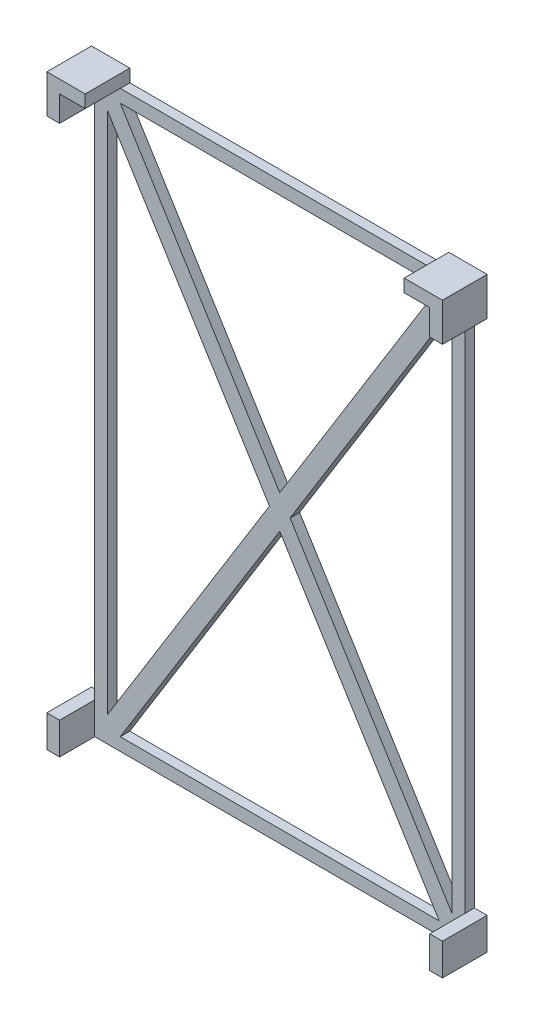
SolidWorks part; units mm, degrees
ref_plane "Alzado" through (0, 0, 0) normal (0, 0, 1) x (1, 0, 0)
ref_plane "Planta" through (0, 0, 0) normal (0, 1, 0) x (1, 0, 0)
ref_plane "Vista lateral" through (0, 0, 0) normal (1, 0, 0) x (0, 0, -1)
sketch "Croquis1" plane through (0, 0, 0) normal (0, 0, 1) x (1, 0, 0)
  line L1 (-96.0018, 29.9441) -> (-38.0018, 29.9441)
  line L2 (-96.0018, 29.9441) -> (-96.0018, -60.0559)
  line L3 (-96.0018, -60.0559) -> (-38.0018, -60.0559)
  line L4 (-38.0018, 29.9441) -> (-38.0018, -60.0559)
  line L5 (-94.0018, 27.9441) -> (-40.0018, 27.9441)
  line L6 (-94.0018, 27.9441) -> (-94.0018, -58.0559)
  line L7 (-94.0018, -58.0559) -> (-40.0018, -58.0559)
  line L8 (-40.0018, 27.9441) -> (-40.0018, -58.0559)
  dimension "D1" = 90
  dimension "D2" = 58
  dimension "D3" = 2
  dimension "D4" = 2
  dimension "D5" = 2
  dimension "D6" = 2
extrude "Saliente-Extruir1" add sketch "Croquis1" along normal blind 1.5
sketch "Croquis2" plane through (0, 0, 0) normal (0, 0, -1) x (-1, 0, 0)
  line L0 (67.0018, -60.0559) -> (67.0018, -58.0559) construction
  line L1 (38.0018, -60.0559) -> (36.0018, -60.0559)
  line L2 (38.0018, -60.0559) -> (38.0018, -55.0559)
  line L3 (38.0018, -55.0559) -> (36.0018, -55.0559)
  line L4 (36.0018, -60.0559) -> (36.0018, -55.0559)
  line L5 (96.0018, -60.0559) -> (38.0018, -60.0559) construction
  line L6 (94.0018, -58.0559) -> (40.0018, -58.0559) construction
  line L7 (38.0018, 29.9441) -> (38.0018, 25.9441)
  line L8 (38.0018, -60.0559) -> (38.0018, 29.9441) construction
  line L9 (38.0018, 25.9441) -> (36.0018, 25.9441)
  line L10 (36.0018, 25.9441) -> (36.0018, 31.9441)
  line L11 (36.0018, 31.9441) -> (42.0018, 31.9441)
  line L12 (42.0018, 31.9441) -> (42.0018, 29.9441)
  line L13 (38.0018, 29.9441) -> (96.0018, 29.9441) construction
  line L14 (42.0018, 29.9441) -> (38.0018, 29.9441)
  line L15 (92.0018, 29.9441) -> (96.0018, 29.9441)
  line L16 (92.0018, 31.9441) -> (92.0018, 29.9441)
  line L17 (98.0018, 31.9441) -> (92.0018, 31.9441)
  line L18 (98.0018, 25.9441) -> (98.0018, 31.9441)
  line L19 (96.0018, 25.9441) -> (98.0018, 25.9441)
  line L20 (96.0018, 29.9441) -> (96.0018, 25.9441)
  line L21 (98.0018, -60.0559) -> (98.0018, -55.0559)
  line L22 (96.0018, -55.0559) -> (98.0018, -55.0559)
  line L23 (96.0018, -60.0559) -> (96.0018, -55.0559)
  line L24 (96.0018, -60.0559) -> (98.0018, -60.0559)
  dimension "D1" = 5
  dimension "D2" = 2
  dimension "D3" = 2
  dimension "D4" = 2
  dimension "D5" = 6
  dimension "D6" = 6
extrude "Saliente-Extruir2" add sketch "Croquis2" against normal blind 7
sketch "Croquis3" plane through (0, 0, 0) normal (0, 0, -1) x (-1, 0, 0)
  line L0 (40.0018, 27.9441) -> (40.0018, 25.9441) construction
  line L1 (40.0018, -58.0559) -> (40.0018, 27.9441) construction
  line L2 (40.0018, 27.9441) -> (42.0018, 27.9441) construction
  line L3 (40.0018, 27.9441) -> (94.0018, 27.9441) construction
  line L4 (94.0018, -58.0559) -> (94.0018, -56.0559) construction
  line L5 (94.0018, 27.9441) -> (94.0018, -58.0559) construction
  line L6 (94.0018, -58.0559) -> (92.0018, -58.0559) construction
  line L7 (94.0018, -58.0559) -> (40.0018, -58.0559) construction
  line L8 (94.0018, -56.0559) -> (68.6208, -15.0559)
  line L9 (42.0018, 27.9441) -> (40.0018, 27.9441)
  line L10 (40.0018, 27.9441) -> (40.0018, 25.9441)
  line L11 (40.0018, 25.9441) -> (65.3827, -15.0559)
  line L12 (92.0018, -58.0559) -> (94.0018, -58.0559)
  line L13 (94.0018, -58.0559) -> (94.0018, -56.0559)
  line L14 (40.0018, -58.0559) -> (40.0018, -56.0559)
  line L15 (40.0018, -58.0559) -> (42.0018, -58.0559)
  line L16 (68.6208, -15.0559) -> (94.0018, 25.9441)
  line L17 (94.0018, 25.9441) -> (94.0018, 27.9441)
  line L18 (94.0018, 27.9441) -> (92.0018, 27.9441)
  line L19 (92.0018, 27.9441) -> (67.0018, -12.4405)
  line L20 (42.0018, 27.9441) -> (67.0018, -12.4405)
  line L21 (40.0018, -56.0559) -> (65.3827, -15.0559)
  line L22 (92.0018, -58.0559) -> (67.0018, -17.6713)
  line L23 (42.0018, -58.0559) -> (67.0018, -17.6713)
extrude "Saliente-Extruir3" add sketch "Croquis3" against normal up to vertex
